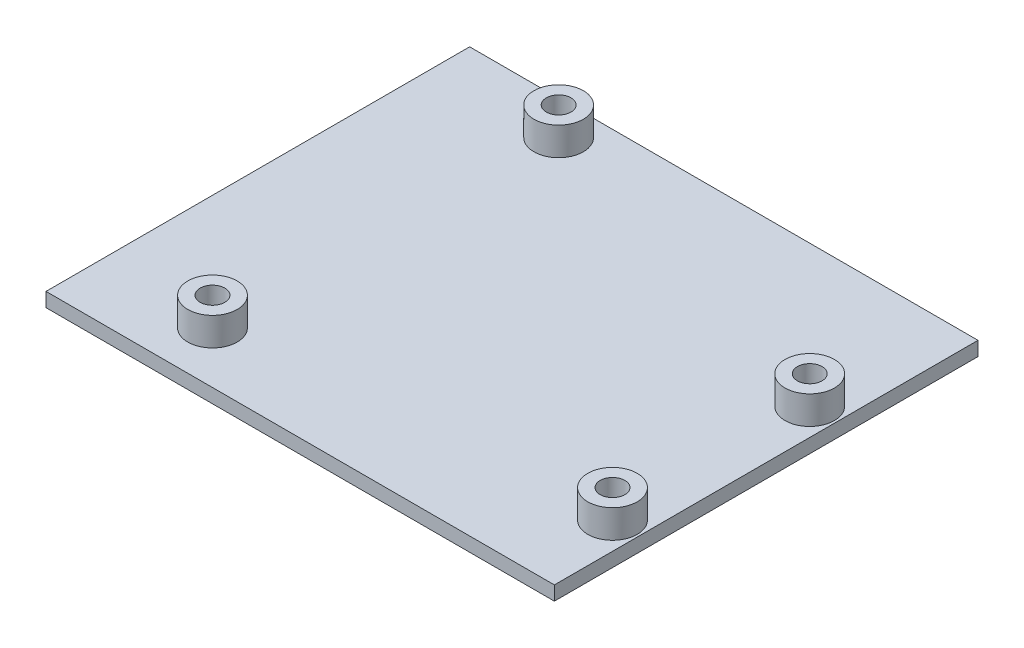
SolidWorks part; units mm, degrees
ref_plane "Plan de face" through (0, 0, 0) normal (0, 0, 1) x (1, 0, 0)
ref_plane "Plan de dessus" through (0, 0, 0) normal (0, 1, 0) x (1, 0, 0)
ref_plane "Plan de droite" through (0, 0, 0) normal (1, 0, 0) x (0, 0, -1)
sketch "Esquisse1" plane through (0, 0, 0) normal (0, 1, 0) x (1, 0, 0)
  line L1 (36, 30) -> (-36, 30)
  line L2 (36, 30) -> (36, -30)
  line L3 (36, -30) -> (-36, -30)
  line L4 (-36, 30) -> (-36, -30)
  line L5 (36, 30) -> (-36, -30) construction
  line L6 (36, -30) -> (-36, 30) construction
  point P0 (0, 0)
  dimension "D1" = 60
  dimension "D2" = 72
extrude "Boss.-Extru.1" add sketch "Esquisse1" along normal blind 2
sketch "Esquisse3" plane through (0, 2, 0) normal (0, 1, 0) x (1, 0, 0)
  circle A0 centre (-19.742, -22.6773) radius 3.5
  circle A1 centre (32.177, -17.9412) radius 3.5
  circle A2 centre (32.1808, 9.9866) radius 3.5
  circle A3 centre (-18.5648, 25.1733) radius 3.5
  dimension "D1" = 7
  dimension "D2" = 7
  dimension "D3" = 7
  dimension "D4" = 7
extrude "Boss.-Extru.2" add sketch "Esquisse3" along normal blind 4
sketch "Esquisse2" plane through (0, 2, 0) normal (0, 1, 0) x (1, 0, 0)
  circle A0 centre (-18.5648, 25.1733) radius 1.75
  circle A1 centre (32.1808, 9.9866) radius 1.75
  circle A2 centre (32.177, -17.9412) radius 1.75
  circle A3 centre (-19.742, -22.6773) radius 1.75
  dimension "D1" = 3.5
  dimension "D2" = 3.5
  dimension "D3" = 3.5
  dimension "D4" = 3.5
extrude "Enlèv. mat.-Extru.1" cut sketch "Esquisse2" along normal blind 4
